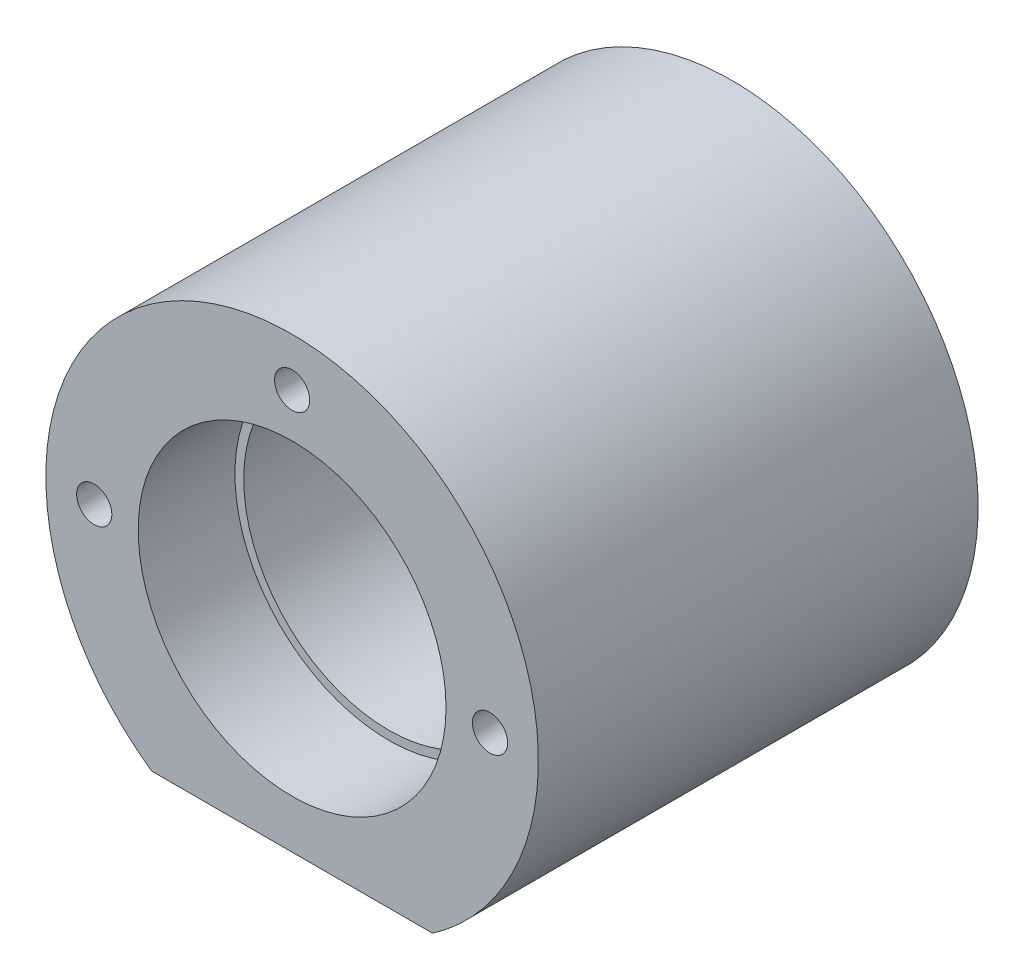
SolidWorks part; units mm, degrees
material "6061 Alloy"
ref_plane "Front Plane" through (0, 0, 0) normal (0, 0, 1) x (1, 0, 0)
ref_plane "Top Plane" through (0, 0, 0) normal (0, 1, 0) x (1, 0, 0)
ref_plane "Right Plane" through (0, 0, 0) normal (1, 0, 0) x (0, 0, -1)
sketch "Sketch1" plane through (0, 0, 0) normal (0, 0, 1) x (1, 0, 0)
  line L0 (-15.9687, 0) -> (15.9687, 0)
  arc A0 (15.9687, 0) -> (-15.9687, 0) centre (0, 23) ccw
  circle A1 centre (0, 23) radius 16.5
  dimension "D2" = 56
  dimension "D3" = 33
  dimension "D1" = 23
extrude "Boss-Extrude1" add sketch "Sketch1" along normal blind 50
sketch "Sketch2" plane through (0, 0, 50) normal (0, 0, 1) x (1, 0, 0)
  circle A0 centre (0, 23) radius 17.5
  arc A1 (15.9687, 0) -> (-15.9687, 0) centre (0, 23) ccw construction
  dimension "D1" = 35
extrude "Cut-Extrude1" cut sketch "Sketch2" against normal blind 11
ref_plane "Plane1" through (0, 0, 25) normal (0, 0, 1) x (1, 0, 0)
mirror "Mirror1" about plane through (0, 0, 25) normal (0, 0, 1) of "Cut-Extrude1"
sketch "Sketch3" plane through (0, 0, 0) normal (0, 0, -1) x (-1, 0, 0)
  circle A0 centre (0, 23) radius 16.5 construction
  circle A1 centre (0, 45.5) radius 2
  circle A2 centre (-22.5, 23) radius 2
  circle A3 centre (22.5, 23) radius 2
  point P0 (0, 23)
  point P9 (0, 0)
  point P10 (0, 0)
  point P11 (0, 0)
  point P14 (20.0806, 22.9231)
  dimension "D4" = 4
  dimension "D1" = 22.5
  dimension "D2" = 22.5
  dimension "D3" = 22.5
extrude "Cut-Extrude2" cut sketch "Sketch3" against normal blind 10
mirror "Mirror2" about plane through (0, 0, 25) normal (0, 0, 1) of "Cut-Extrude2"
